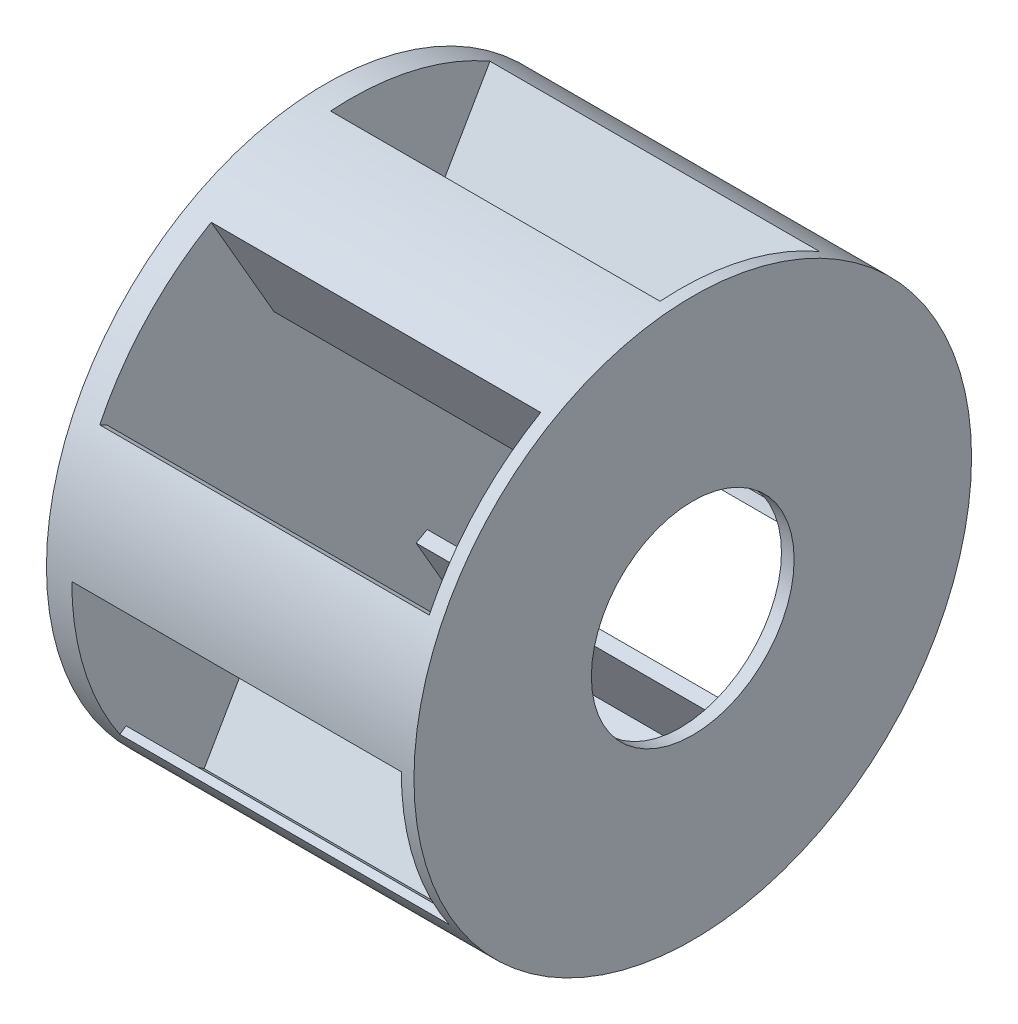
SolidWorks part; units mm, degrees
ref_plane "Front Plane" through (0, 0, 0) normal (0, 0, 1) x (1, 0, 0)
ref_plane "Top Plane" through (0, 0, 0) normal (0, 1, 0) x (1, 0, 0)
ref_plane "Right Plane" through (0, 0, 0) normal (1, 0, 0) x (0, 0, -1)
sketch "Sketch1" plane through (0, 0, 0) normal (1, 0, 0) x (0, 0, -1)
  circle A0 centre (0, 0) radius 5.5
  dimension "D1" = 11
extrude "Boss-Extrude1" add sketch "Sketch1" along normal blind 0.5
sketch "Sketch2" plane through (0.5, 0, 0) normal (1, 0, 0) x (0, 0, -1)
  line L0 (-5.5, 0) -> (-3.02, 0)
  line L2 (-3.02, 0.25) -> (-3.02, 0)
  line L3 (-4.9487, 2.4) -> (-4.8138, 2.3345)
  line L4 (-5.3442, 0.25) -> (-3.02, 0.25)
  arc A0 (-5.5, 0) -> (-4.9487, 2.4) centre (0, 0) cw
  circle A1 centre (0, 0) radius 5.5 construction
  arc A2 (-5.3442, 0.25) -> (-4.8138, 2.3345) centre (0, 0) cw
  arc A3 (-5.35, 0) -> (-4.8138, 2.3345) centre (0, 0) cw construction
  dimension "D1" = 2.48
  dimension "D2" = 2.4
  dimension "D3" = 0.15
extrude "Boss-Extrude2" add sketch "Sketch2" along normal blind 6.5
pattern_circular "CirPattern1" count 6 over 360 about axis through (0, 0, 0) along (1, 0, 0) of "Boss-Extrude2"
sketch "Sketch3" plane through (7, 0, 0) normal (1, 0, 0) x (0, 0, -1)
  circle A0 centre (0, 0) radius 5.5
  circle A1 centre (0, 0) radius 2
  dimension "D1" = 4
extrude "Boss-Extrude3" add sketch "Sketch3" along normal blind 0.25
sketch "Sketch4" plane through (0, 0, 0) normal (-1, 0, 0) x (0, 0, 1)
  circle A0 centre (0, 0) radius 1.5
  circle A1 centre (0, 0) radius 0.75
  dimension "D1" = 1.5
  dimension "D2" = 3
extrude "Boss-Extrude4" add sketch "Sketch4" along normal blind 2.5
